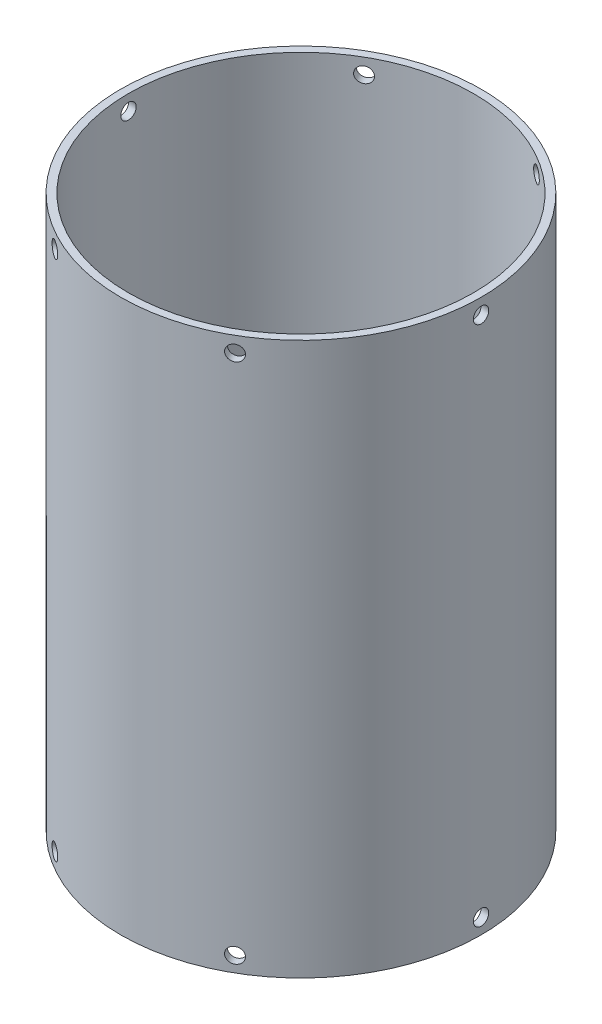
SolidWorks part; units mm, degrees
material "6061-T6 (SS)"
ref_plane "Front Plane" through (0, 0, 0) normal (0, 0, 1) x (1, 0, 0)
ref_plane "Top Plane" through (0, 0, 0) normal (0, 1, 0) x (1, 0, 0)
ref_plane "Right Plane" through (0, 0, 0) normal (1, 0, 0) x (0, 0, -1)
sketch "Sketch1" plane through (0, 0, 0) normal (0, 1, 0) x (1, 0, 0)
  circle A0 centre (0, 0) radius 149.225
  circle A1 centre (0, 0) radius 142.875
  dimension "D1" = 298.45
  dimension "D2" = 285.75
extrude "Boss-Extrude1" add sketch "Sketch1" along normal blind 457.2
ref_plane "Plane1" through (149.225, 0, 0) normal (1, 0, 0) x (0, 0, -1)
hole_wizard "1/2 (0.5) Diameter Hole1" positions "Sketch2" profile "Sketch3" hole size "1/2" standard "ANSI Inch"
sketch "Sketch2" plane through (149.225, 0, 0) normal (1, 0, 0) x (0, 0, -1)
  line L0 (0, 164.1475) -> (0, -164.1475) construction
  line L1 (149.225, 457.2) -> (-149.225, 457.2) construction
  point P0 (0, 444.5)
  dimension "D1" = 12.7
sketch "Sketch3" plane through (149.225, 444.5, 0) normal (0, 1, 0) x (0, 0, -1)
  line L0 (0, 0) -> (0, 344.3972)
  line L1 (0, 344.3972) -> (6.35, 344.3972)
  line L2 (6.35, 344.3972) -> (6.35, 0)
  line L5 (6.35, 0) -> (0, 0)
  line L11 (0, -6.35) -> (0, 107.95) construction
  dimension "Thru Hole Dia." = 12.7
  dimension "Thru Hole Depth" = 344.3972
pattern_circular "CirPattern1" count 6 over 360 about axis through (0, 457.2, 0) along (0, 1, 0) of "1/2 (0.5) Diameter Hole1"
ref_plane "Plane2" through (0, 228.6, 0) normal (0, 1, 0) x (1, 0, 0)
mirror "Mirror1" about plane through (0, 228.6, 0) normal (0, 1, 0) of "CirPattern1", "1/2 (0.5) Diameter Hole1"
